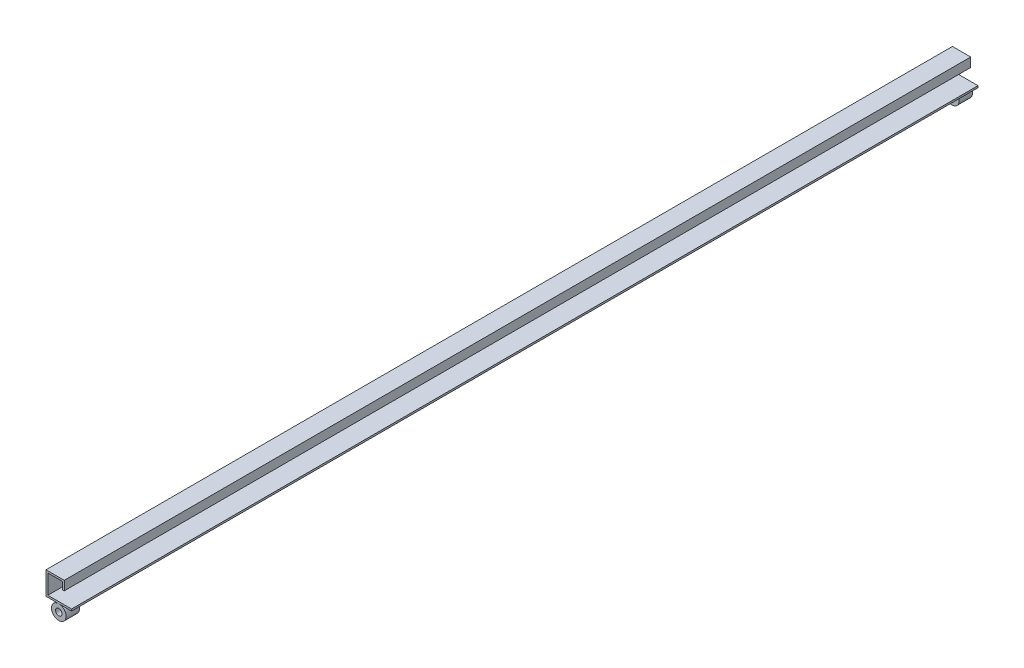
SolidWorks part; units mm, degrees
material "acier chariot"
ref_plane "Front Plane" through (0, 0, 0) normal (0, 0, 1) x (1, 0, 0)
ref_plane "Top Plane" through (0, 0, 0) normal (0, 1, 0) x (1, 0, 0)
ref_plane "Right Plane" through (0, 0, 0) normal (1, 0, 0) x (0, 0, -1)
sketch "Sketch1" plane through (0, 0, 0) normal (0, 0, 1) x (1, 0, 0)
  line L0 (0, 0) -> (-28, 0)
  line L1 (-28, 0) -> (-28, 25.2)
  line L2 (-28, 25.2) -> (-8, 25.2)
  line L3 (-8, 25.2) -> (-8, 15.2)
  line L4 (0, 2) -> (-26, 2)
  line L5 (-26, 2) -> (-26, 23.2)
  line L6 (-26, 23.2) -> (-10, 23.2)
  line L7 (-10, 23.2) -> (-10, 15.2)
  line L8 (-10, 15.2) -> (-8, 15.2)
  line L9 (0, 2) -> (0, 0)
  dimension "D1" = 28
  dimension "D2" = 25.2
  dimension "D3" = 20
  dimension "D4" = 10
  dimension "D5" = 2
extrude "Boss-Extrude1" add sketch "Sketch1" along normal blind 993
sketch "Sketch2" plane through (0, 0, 0) normal (0, 0, -1) x (-1, 0, 0)
  line L0 (14, -12.2654) -> (14, 27.5703) construction
  line L1 (28, 0) -> (0, 0) construction
  circle A0 centre (14, -8) radius 8
  circle A1 centre (14, -8) radius 3.5
  point P8 (14, 0)
  dimension "D1" = 16
  dimension "D2" = 7
extrude "Boss-Extrude2" add sketch "Sketch2" against normal blind 14.6 separate body
ref_plane "Plane1" through (0, 0, 496.5) normal (0, 0, -1) x (-1, 0, 0)
mirror "Mirror10" about plane through (0, 0, 496.5) normal (0, 0, -1) of bodies 102
